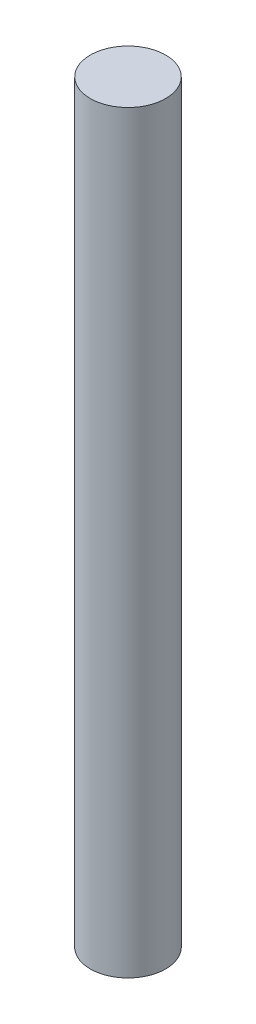
SolidWorks part; units mm, degrees
material "Stainless Steel (ferritic)"
ref_plane "Front Plane" through (0, 0, 0) normal (0, 0, 1) x (1, 0, 0)
ref_plane "Top Plane" through (0, 0, 0) normal (0, 1, 0) x (1, 0, 0)
ref_plane "Right Plane" through (0, 0, 0) normal (1, 0, 0) x (0, 0, -1)
sketch "Sketch1" plane through (0, 0, 0) normal (0, 1, 0) x (1, 0, 0)
  circle A0 centre (0, 0) radius 20
extrude "Boss-Extrude1" add sketch "Sketch1" along normal blind 400
scale "Scale1" scale about centroid uniform scaling yes scale factor 0.125
